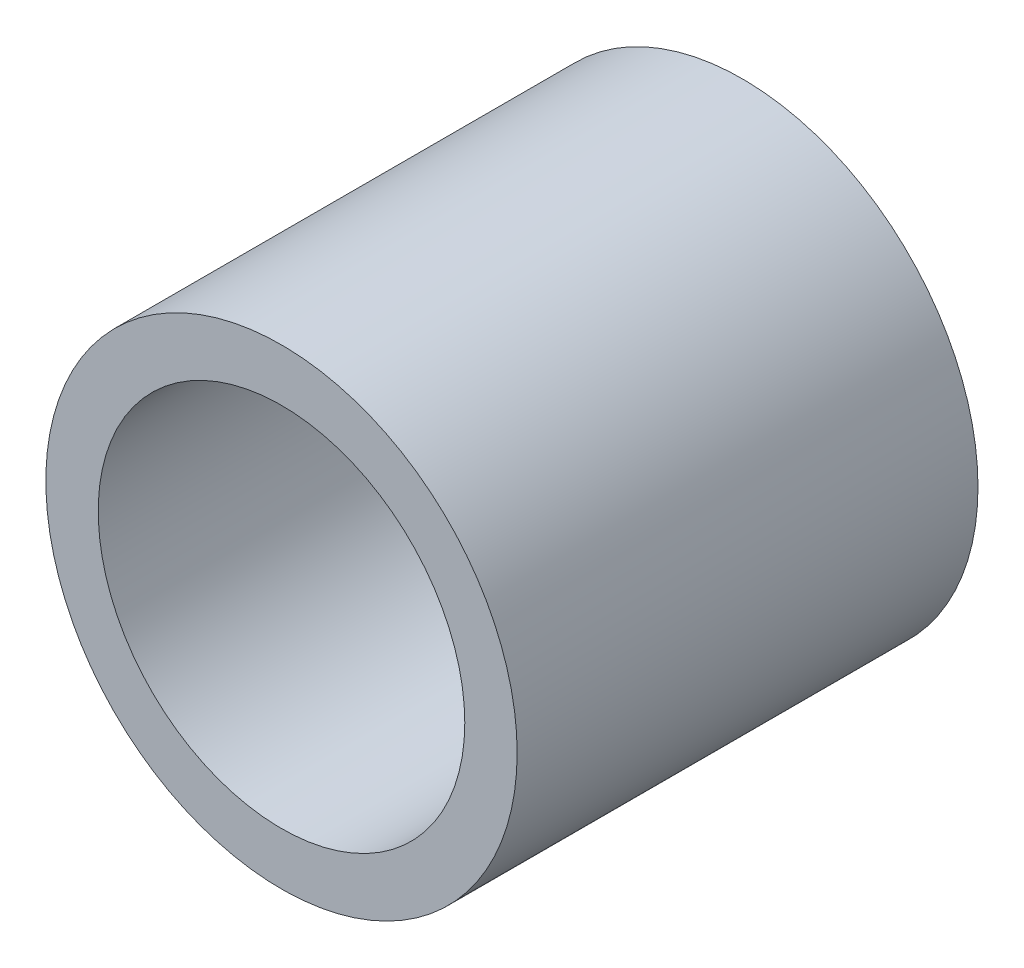
SolidWorks part; units mm, degrees
ref_plane "Plan de face" through (0, 0, 0) normal (0, 0, 1) x (1, 0, 0)
ref_plane "Plan de dessus" through (0, 0, 0) normal (0, 1, 0) x (1, 0, 0)
ref_plane "Plan de droite" through (0, 0, 0) normal (1, 0, 0) x (0, 0, -1)
sketch "Esquisse1" plane through (0, 0, 0) normal (0, 0, 1) x (1, 0, 0)
  circle A0 centre (0, 0) radius 4.375
  circle A1 centre (0, 0) radius 5.625
extrude "Extrusion1" add sketch "Esquisse1" along normal blind 11
